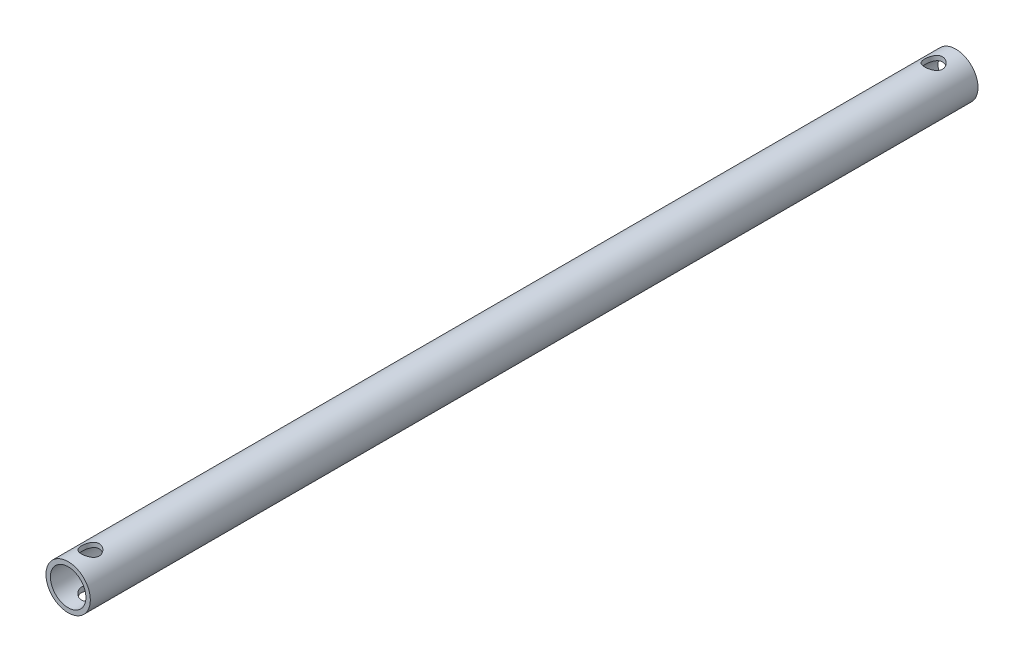
SolidWorks part; units mm, degrees
material "普通碳钢"
ref_plane "前视基准面" through (0, 0, 0) normal (0, 0, 1) x (1, 0, 0)
ref_plane "上视基准面" through (0, 0, 0) normal (0, 1, 0) x (1, 0, 0)
ref_plane "右视基准面" through (0, 0, 0) normal (1, 0, 0) x (0, 0, -1)
sketch "草图1" plane through (0, 0, 0) normal (0, 0, 1) x (1, 0, 0)
  circle A0 centre (0, 0) radius 8
  circle A1 centre (0, 0) radius 10
  dimension "D1" = 16
  dimension "D2" = 20
extrude "凸台-拉伸1" add sketch "草图1" along normal blind 400
sketch "草图2" plane through (0, 0, 0) normal (0, 1, 0) x (1, 0, 0)
  line L0 (0, 0) -> (0, -20) construction
  line L1 (8, 0) -> (-8, 0) construction
  line L2 (0, -400) -> (0, -825.7248) construction
  line L3 (-10, -400) -> (10, -400) construction
  circle A0 centre (0, -10) radius 4
  circle A1 centre (0, -390) radius 4
  dimension "D1" = 8
  dimension "D3" = 8
  dimension "D2" = 10
  dimension "D4" = 10
extrude "切除-拉伸1" cut sketch "草图2" against normal through all and the other way through all
